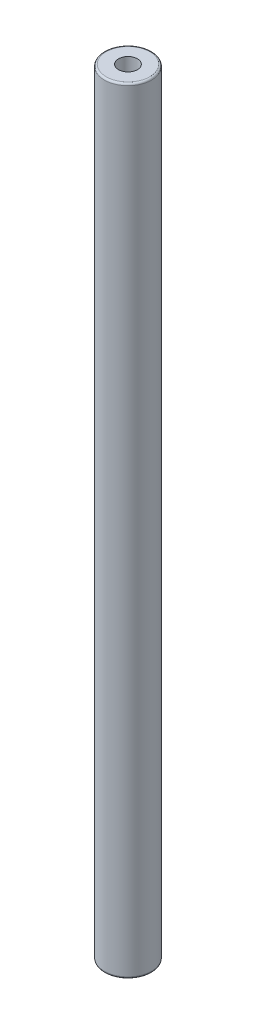
SolidWorks part; units mm, degrees
ref_plane "Front Plane" through (0, 0, 0) normal (0, 0, 1) x (1, 0, 0)
ref_plane "Top Plane" through (0, 0, 0) normal (0, 1, 0) x (1, 0, 0)
ref_plane "Right Plane" through (0, 0, 0) normal (1, 0, 0) x (0, 0, -1)
sketch "Sketch3" plane through (0, 0, 0) normal (1, 0, 0) x (0, 0, -1)
  line L0 (0, 41) -> (0, -41)
  line L1 (0, 41) -> (2.5, 41)
  line L2 (2.5, 41) -> (2.5, -41)
  line L3 (2.5, -41) -> (0, -41)
  point P4 (0, 0)
  dimension "D1" = 82
  dimension "D2" = 2.5
revolve "Revolve2" add sketch "Sketch3" angle 360 about L0
sketch "Sketch4" plane through (0, 41, 0) normal (0, 1, 0) x (1, 0, 0)
  circle A0 centre (0, 0) radius 1
  dimension "D1" = 2
extrude "Cut-Extrude1" cut sketch "Sketch4" against normal blind 82
fillet "Fillet1" radius 0.2 2 edges at (0, -41, 2.5) (0, 41, 2.5)
